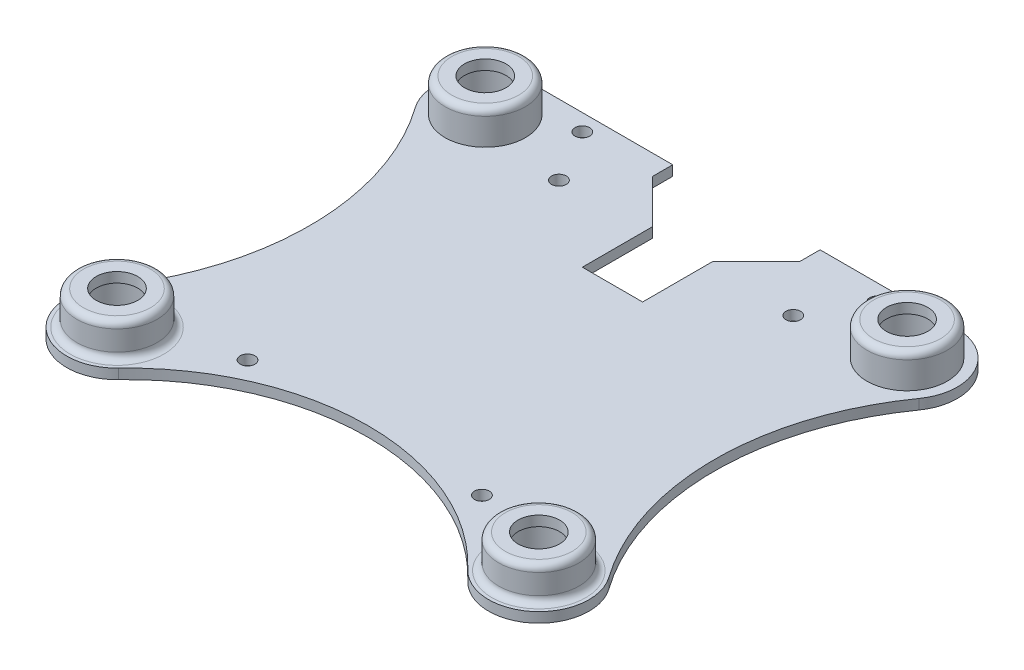
SolidWorks part; units mm, degrees
material "Sculpteo SLS"
ref_plane "Front Plane" through (0, 0, 0) normal (0, 0, 1) x (1, 0, 0)
ref_plane "Top Plane" through (0, 0, 0) normal (0, 1, 0) x (1, 0, 0)
ref_plane "Right Plane" through (0, 0, 0) normal (1, 0, 0) x (0, 0, -1)
sketch "Sketch1" plane through (0, 0, 0) normal (0, 1, 0) x (1, 0, 0)
  line L0 (0, 0) -> (0, -14730.86) construction
  line L1 (0, 0) -> (-50000, 0) construction
  line L2 (-31.5, 37.5) -> (31.5, 37.5)
  arc A0 (-37.6152, -20.6579) -> (-26.069, -30.1724) centre (-31.5, -25) ccw
  arc A1 (26.069, -30.1724) -> (37.6152, -20.6579) centre (31.5, -25) ccw
  arc A2 (37.6152, 25.6579) -> (31.5, 37.5) centre (31.5, 30) ccw
  arc A3 (-31.5, 37.5) -> (-37.6152, 25.6579) centre (-31.5, 30) ccw
  arc A4 (37.6152, 25.6579) -> (37.6152, -20.6579) centre (70.2298, 2.5) ccw
  arc A5 (-37.6152, 25.6579) -> (-37.6152, -20.6579) centre (-70.2298, 2.5) cw
  arc A6 (26.069, -30.1724) -> (-26.069, -30.1724) centre (0, -55) ccw
  dimension "D1" = 63
  dimension "D2" = 15
  dimension "D6" = 55
  dimension "D7" = 55
  dimension "D5" = 40
  dimension "D3" = 30
  dimension "D4" = 63
extrude "Boss-Extrude1" add sketch "Sketch1" along normal blind 1.5
sketch "Sketch2" plane through (0, 1.5, 0) normal (0, 1, 0) x (1, 0, 0)
  line L0 (0, -49997) -> (0, -50000) construction
  line L1 (31.5, 37.5) -> (-31.5, 37.5) construction
  line L2 (-11, 37.5) -> (11, 37.5)
  line L3 (-11, 37.5) -> (-11, 34.5)
  line L5 (11, 37.5) -> (11, 34.5)
  line L6 (-11, 34.5) -> (-4.5, 28)
  line L7 (-4.5, 28) -> (-4.5, 17.5)
  line L8 (-4.5, 17.5) -> (4.5, 17.5)
  line L9 (4.5, 28) -> (4.5, 17.5)
  line L10 (11, 34.5) -> (4.5, 28)
  point P13 (0, 17.5)
  dimension "D1" = 22
  dimension "D2" = 3
  dimension "D3" = 4.5
  dimension "D4" = 9.5
  dimension "D5" = 10.5
extrude "Cut-Extrude1" cut sketch "Sketch2" against normal through all
sketch "Sketch6" plane through (0, 1.5, 0) normal (0, 1, 0) x (1, 0, 0)
  circle A0 centre (-31.5, 30) radius 6
  circle A1 centre (31.5, 30) radius 6
  circle A2 centre (-31.5, -25) radius 6
  circle A3 centre (31.5, -25) radius 6
  dimension "D1" = 12
extrude "Boss-Extrude3" add sketch "Sketch6" along normal blind 5
sketch "Sketch3" plane through (0, 1.5, 0) normal (0, 1, 0) x (1, 0, 0)
  circle A0 centre (-31.5, 30) radius 3.1
  circle A1 centre (31.5, 30) radius 3.1
  circle A2 centre (31.5, -25) radius 3.1
  circle A3 centre (-31.5, -25) radius 3.1
  dimension "D1" = 6.2
extrude "Cut-Extrude2" cut sketch "Sketch3" against normal through all and the other way through all
sketch "Sketch4" plane through (0, 1.5, 0) normal (0, 1, 0) x (1, 0, 0)
  line L0 (-11, 37.5) -> (-31.5, 37.5) construction
  line L1 (0, 0) -> (0, -50000) construction
  circle A0 centre (-17.5, 27) radius 1.1
  circle A1 centre (17.5, 27) radius 1.1
  circle A2 centre (-22, 35) radius 1.1
  circle A3 centre (22, 35) radius 1.1
  circle A4 centre (-17.5, -19.5) radius 1.1
  circle A5 centre (17.5, -19.5) radius 1.1
  dimension "D1" = 2.2
  dimension "D2" = 35
  dimension "D3" = 10.5
  dimension "D4" = 44
  dimension "D5" = 2.5
  dimension "D6" = 46.5
extrude "Cut-Extrude3" cut sketch "Sketch4" against normal through all
sketch "Sketch7" plane through (0, 0, 0) normal (0, -1, 0) x (1, 0, 0)
  circle A0 centre (-31.5, -30) radius 4.5
  circle A1 centre (31.5, -30) radius 4.5
  circle A2 centre (-31.5, 25) radius 4.5
  circle A3 centre (31.5, 25) radius 4.5
  dimension "D1" = 9
extrude "Cut-Extrude5" cut sketch "Sketch7" against normal offset from surface (5 mm away) 1.5 up to face at (-31.5, 6.5, -26.9)
fillet "Fillet1" radius 1 6 edges at (-31.5, 6.5, -24) (-31.5, 1.5, 31) (31.5, 1.5, 31) (-31.5, 6.5, 31) (31.5, 6.5, 31) (31.5, 6.5, -24)
